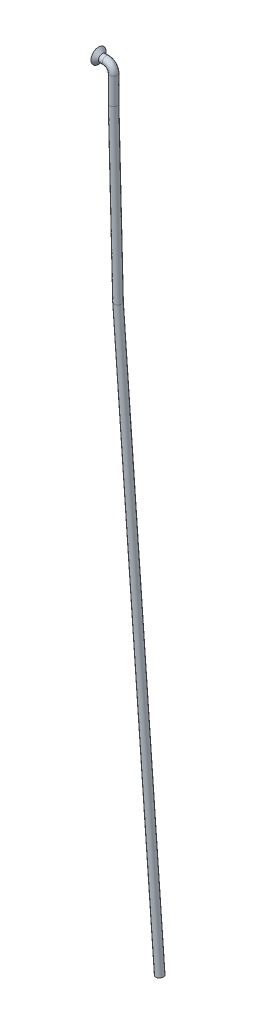
SolidWorks part; units mm, degrees
ref_plane "Plan de face" through (0, 0, 0) normal (0, 0, 1) x (1, 0, 0)
ref_plane "Plan de dessus" through (0, 0, 0) normal (0, 1, 0) x (1, 0, 0)
ref_plane "Plan de droite" through (0, 0, 0) normal (1, 0, 0) x (0, 0, -1)
sketch "Esquisse1" plane through (0, 0, 0) normal (0, 0, 1) x (1, 0, 0)
  line L0 (1.178, -53.9846) -> (12.228, -203.0321)
  line L1 (-2, 0) -> (-4, 0)
  line L2 (0, -2) -> (0, -9)
  line L3 (0, -9) -> (1.178, -53.9846)
  arc A0 (0, -2) -> (-2, 0) centre (-2, -2) ccw
  point P6 (0, 0)
  dimension "D3" = 2
  dimension "D1" = 4
  dimension "D2" = 91.5
  dimension "D4" = 203.4
  dimension "D5" = 7
  dimension "D6" = 45
  dimension "D7" = 11.05
ref_plane "Plan1" through (-4, 0, 0) normal (1, 0, 0) x (0, 0, -1)
sketch "Esquisse2" plane through (-4, 0, 0) normal (1, 0, 0) x (0, 0, -1)
  circle A0 centre (0, 0) radius 1
  dimension "D1" = 2
sweep "Balayage1" add profiles "Esquisse2" path "Esquisse1"
sketch "Esquisse3" plane through (0, 0, 0) normal (0, 0, 1) x (1, 0, 0)
  line L0 (-4, 1) -> (-4, 2)
  line L1 (-4, 2) -> (-3, 1)
  line L2 (-3, 1) -> (-4, 1)
  line L3 (-2, 1) -> (-4, 1) construction
  line L4 (-4, 1) -> (-4, -1) construction
  line L5 (0, 0) -> (-9.5023, 0) construction
  line L6 (-2, 0) -> (-4, 0) construction
  dimension "D1" = 4
  dimension "D2" = 1
revolve "Révolution1" add sketch "Esquisse3" angle 360 about L5
